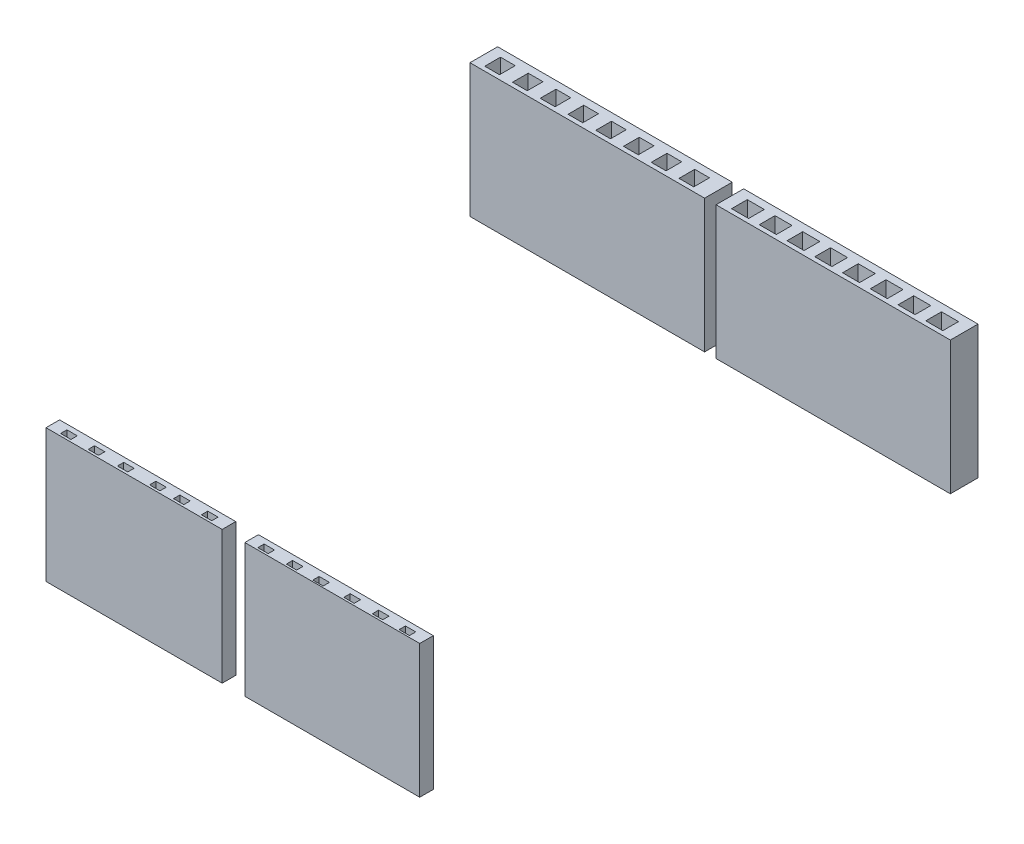
SolidWorks part; units mm, degrees
ref_plane "Alzado" through (0, 0, 0) normal (0, 0, 1) x (1, 0, 0)
ref_plane "Planta" through (0, 0, 0) normal (0, 1, 0) x (1, 0, 0)
ref_plane "Vista lateral" through (0, 0, 0) normal (1, 0, 0) x (0, 0, -1)
sketch "Croquis1" plane through (0, 32.4682, 0) normal (0, 1, 0) x (1, 0, 0)
  line L0 (35.019, -74.2465) -> (50.7771, -74.2465)
  line L1 (50.7771, -74.2465) -> (50.7771, -75.4707)
  line L2 (-14.2075, -75.4707) -> (51.0035, -75.4707) construction
  line L3 (50.7771, -75.4707) -> (35.019, -75.4707)
  line L4 (35.019, -75.4707) -> (35.019, -74.2465)
  line L5 (7.7243, -25.4005) -> (28.8613, -25.4005)
  line L6 (28.8613, -25.4005) -> (28.8613, -27.8923)
  line L7 (28.8613, -27.8923) -> (7.7243, -27.8923)
  line L8 (7.7243, -27.8923) -> (7.7243, -25.4005)
  line L9 (29.8924, -25.4005) -> (51.0035, -25.4005)
  line L10 (51.0035, -35.9939) -> (51.0035, -24.4939) construction
  line L11 (51.0035, -25.4005) -> (51.0035, -27.8923)
  line L12 (51.0035, -27.8923) -> (29.8924, -27.8923)
  line L13 (29.8924, -27.8923) -> (29.8924, -25.4005)
  line L14 (32.9767, -75.4707) -> (32.9767, -74.2465)
  line L15 (32.9767, -74.2465) -> (17.1043, -74.2465)
  line L16 (17.1043, -74.2465) -> (17.1043, -75.4707)
  line L17 (17.1043, -75.4707) -> (32.9767, -75.4707)
  line L18 (38.5729, -74.7194) -> (39.5063, -74.7194)
  line L19 (36.0061, -74.7194) -> (36.9394, -74.7194)
  line L20 (36.0061, -74.7194) -> (36.0061, -75.2898)
  line L21 (36.0061, -75.2898) -> (36.9394, -75.2898)
  line L22 (36.9394, -74.7194) -> (36.9394, -75.2898)
  line L23 (38.5729, -75.2898) -> (39.5063, -75.2898)
  line L24 (38.5729, -74.7194) -> (38.5729, -75.2898)
  line L25 (39.5063, -74.7194) -> (39.5063, -75.2898)
  line L26 (41.0101, -74.7713) -> (41.9435, -74.7713)
  line L27 (41.0101, -75.3417) -> (41.9435, -75.3417)
  line L28 (41.0101, -74.7713) -> (41.0101, -75.3417)
  line L29 (41.9435, -74.7713) -> (41.9435, -75.3417)
  line L30 (43.7584, -74.7194) -> (44.6918, -74.7194)
  line L31 (43.7584, -75.2898) -> (44.6918, -75.2898)
  line L32 (43.7584, -74.7194) -> (43.7584, -75.2898)
  line L33 (44.6918, -74.7194) -> (44.6918, -75.2898)
  line L34 (46.3253, -74.7194) -> (47.2587, -74.7194)
  line L35 (46.3253, -75.2898) -> (47.2587, -75.2898)
  line L36 (46.3253, -74.7194) -> (46.3253, -75.2898)
  line L37 (47.2587, -74.7194) -> (47.2587, -75.2898)
  line L38 (48.7625, -74.7454) -> (49.6958, -74.7454)
  line L39 (48.7625, -75.3158) -> (49.6958, -75.3158)
  line L40 (48.7625, -74.7454) -> (48.7625, -75.3158)
  line L41 (49.6958, -74.7454) -> (49.6958, -75.3158)
  line L42 (30.8983, -74.6935) -> (31.8317, -74.6935)
  line L43 (30.8983, -75.2639) -> (31.8317, -75.2639)
  line L44 (30.8983, -74.6935) -> (30.8983, -75.2639)
  line L45 (31.8317, -74.6935) -> (31.8317, -75.2639)
  line L46 (28.3833, -74.6935) -> (29.3167, -74.6935)
  line L47 (28.3833, -75.2639) -> (29.3167, -75.2639)
  line L48 (28.3833, -74.6935) -> (28.3833, -75.2639)
  line L49 (29.3167, -74.6935) -> (29.3167, -75.2639)
  line L50 (26.2313, -74.6935) -> (27.1647, -74.6935)
  line L51 (26.2313, -75.2639) -> (27.1647, -75.2639)
  line L52 (26.2313, -74.6935) -> (26.2313, -75.2639)
  line L53 (27.1647, -74.6935) -> (27.1647, -75.2639)
  line L54 (18.2116, -74.6935) -> (19.145, -74.6935)
  line L55 (18.2116, -75.2639) -> (19.145, -75.2639)
  line L56 (18.2116, -74.6935) -> (18.2116, -75.2639)
  line L57 (19.145, -74.6935) -> (19.145, -75.2639)
  line L58 (20.6958, -74.6935) -> (21.6292, -74.6935)
  line L59 (20.6958, -75.2639) -> (21.6292, -75.2639)
  line L60 (20.6958, -74.6935) -> (20.6958, -75.2639)
  line L61 (21.6292, -74.6935) -> (21.6292, -75.2639)
  line L62 (23.3088, -74.6714) -> (24.2422, -74.6714)
  line L63 (23.3088, -75.2418) -> (24.2422, -75.2418)
  line L64 (23.3088, -74.6714) -> (23.3088, -75.2418)
  line L65 (24.2422, -74.6714) -> (24.2422, -75.2418)
  line L66 (11.1655, -26.0847) -> (11.1655, -27.4995)
  line L67 (8.6655, -26.0847) -> (9.9945, -26.0847)
  line L68 (8.6655, -26.0847) -> (8.6655, -27.4995)
  line L69 (8.6655, -27.4995) -> (9.9945, -27.4995)
  line L70 (9.9945, -26.0847) -> (9.9945, -27.4995)
  line L71 (11.1655, -26.0847) -> (12.4945, -26.0847)
  line L72 (12.4945, -26.0847) -> (12.4945, -27.4995)
  line L73 (11.1655, -27.4995) -> (12.4945, -27.4995)
  line L74 (13.6655, -26.0847) -> (13.6655, -27.4995)
  line L75 (13.6655, -26.0847) -> (14.9945, -26.0847)
  line L76 (14.9945, -26.0847) -> (14.9945, -27.4995)
  line L77 (13.6655, -27.4995) -> (14.9945, -27.4995)
  line L78 (16.1655, -26.0847) -> (16.1655, -27.4995)
  line L79 (16.1655, -26.0847) -> (17.4945, -26.0847)
  line L80 (17.4945, -26.0847) -> (17.4945, -27.4995)
  line L81 (16.1655, -27.4995) -> (17.4945, -27.4995)
  line L82 (18.6655, -26.0847) -> (18.6655, -27.4995)
  line L83 (18.6655, -26.0847) -> (19.9945, -26.0847)
  line L84 (19.9945, -26.0847) -> (19.9945, -27.4995)
  line L85 (18.6655, -27.4995) -> (19.9945, -27.4995)
  line L86 (21.1655, -26.0847) -> (21.1655, -27.4995)
  line L87 (21.1655, -26.0847) -> (22.4945, -26.0847)
  line L88 (22.4945, -26.0847) -> (22.4945, -27.4995)
  line L89 (21.1655, -27.4995) -> (22.4945, -27.4995)
  line L90 (23.6655, -26.0847) -> (23.6655, -27.4995)
  line L91 (23.6655, -26.0847) -> (24.9945, -26.0847)
  line L92 (24.9945, -26.0847) -> (24.9945, -27.4995)
  line L93 (23.6655, -27.4995) -> (24.9945, -27.4995)
  line L94 (26.1655, -26.0847) -> (26.1655, -27.4995)
  line L95 (26.1655, -26.0847) -> (27.4945, -26.0847)
  line L96 (27.4945, -26.0847) -> (27.4945, -27.4995)
  line L97 (26.1655, -27.4995) -> (27.4945, -27.4995)
  line L98 (8.6655, -26.0847) -> (11.1655, -26.0847) construction
  line L99 (33.3983, -26.0847) -> (33.3983, -27.4995)
  line L100 (30.8983, -26.0847) -> (32.433, -26.0847)
  line L101 (30.8983, -26.0847) -> (30.8983, -27.4995)
  line L102 (30.8983, -27.4995) -> (32.433, -27.4995)
  line L103 (32.433, -26.0847) -> (32.433, -27.4995)
  line L104 (33.3983, -26.0847) -> (34.933, -26.0847)
  line L105 (34.933, -26.0847) -> (34.933, -27.4995)
  line L106 (33.3983, -27.4995) -> (34.933, -27.4995)
  line L107 (35.8983, -26.0847) -> (35.8983, -27.4995)
  line L108 (35.8983, -26.0847) -> (37.433, -26.0847)
  line L109 (37.433, -26.0847) -> (37.433, -27.4995)
  line L110 (35.8983, -27.4995) -> (37.433, -27.4995)
  line L111 (38.3983, -26.0847) -> (38.3983, -27.4995)
  line L112 (38.3983, -26.0847) -> (39.933, -26.0847)
  line L113 (39.933, -26.0847) -> (39.933, -27.4995)
  line L114 (38.3983, -27.4995) -> (39.933, -27.4995)
  line L115 (40.8983, -26.0847) -> (40.8983, -27.4995)
  line L116 (40.8983, -26.0847) -> (42.433, -26.0847)
  line L117 (42.433, -26.0847) -> (42.433, -27.4995)
  line L118 (40.8983, -27.4995) -> (42.433, -27.4995)
  line L119 (43.3983, -26.0847) -> (43.3983, -27.4995)
  line L120 (43.3983, -26.0847) -> (44.933, -26.0847)
  line L121 (44.933, -26.0847) -> (44.933, -27.4995)
  line L122 (43.3983, -27.4995) -> (44.933, -27.4995)
  line L123 (45.8983, -26.0847) -> (45.8983, -27.4995)
  line L124 (45.8983, -26.0847) -> (47.433, -26.0847)
  line L125 (47.433, -26.0847) -> (47.433, -27.4995)
  line L126 (45.8983, -27.4995) -> (47.433, -27.4995)
  line L127 (48.3983, -26.0847) -> (48.3983, -27.4995)
  line L128 (48.3983, -26.0847) -> (49.933, -26.0847)
  line L129 (49.933, -26.0847) -> (49.933, -27.4995)
  line L130 (48.3983, -27.4995) -> (49.933, -27.4995)
  line L131 (30.8983, -26.0847) -> (33.3983, -26.0847) construction
  line L132 (51.0035, -25.4005) -> (51.0035, -27.8923)
  dimension "D2" = 2.5
  dimension "D4" = 2.5
  dimension "D1" = 8
  dimension "D3" = 8
extrude "Saliente-Extruir1" add sketch "Croquis1" along normal blind 12 contours L8 L7 L6 L5 L97 L94 L95 L96 L93 L90 L91 L92 L89 L86 L87 L88 L85 L82 L83 L84 L81 L78 L79 L80 L77 L74 L75 L76 L73 L66 L71 L72 L67 L70 L69 L68 | L13 L12 L11 L9 L130 L127 L128 L129 L126 L123 L124 L125 L122 L119 L120 L121 L118 L115 L116 L117 L114 L111 L112 L113 L110 L107 L108 L109 L106 L99 L104 L105 L100 L103 L102 L101 | L16 L17 L14 L15 L58 L61 L59 L60 L50 L53 L51 L52 L42 L45 L43 L44 L46 L49 L47 L48 L54 L57 L55 L56 L62 L65 L63 L64 | L4 L3 L1 L0 L34 L37 L35 L36 L26 L29 L27 L28 L19 L22 L21 L20 L18 L25 L23 L24 L30 L33 L31 L32 L38 L41 L39 L40
